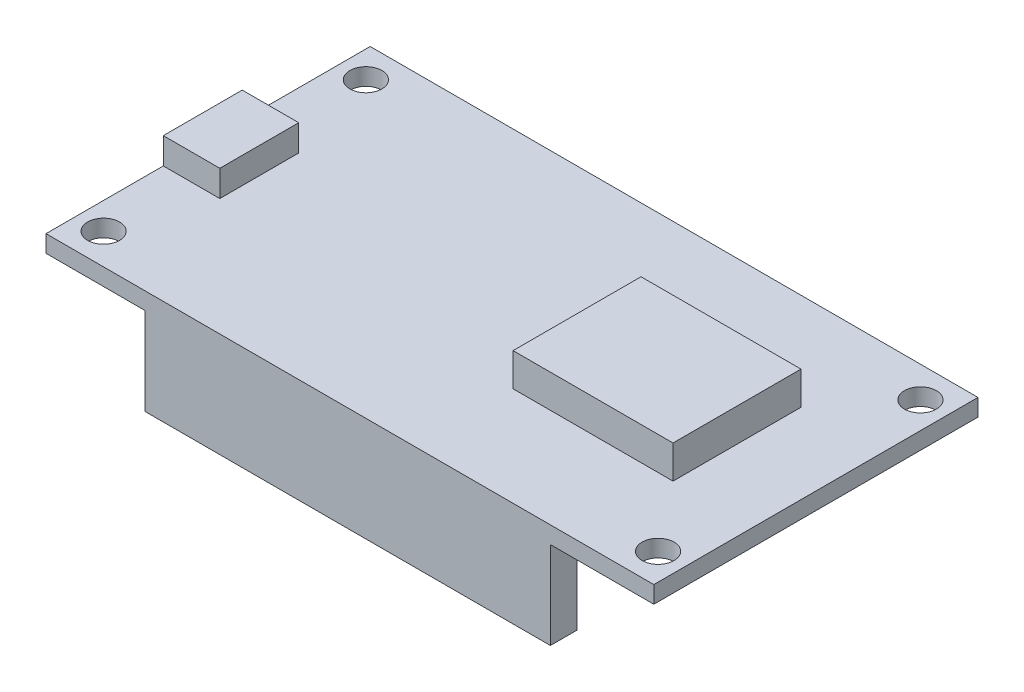
SolidWorks part; units mm, degrees
ref_plane "前视基准面" through (0, 0, 0) normal (0, 0, 1) x (1, 0, 0)
ref_plane "上视基准面" through (0, 0, 0) normal (0, 1, 0) x (1, 0, 0)
ref_plane "右视基准面" through (0, 0, 0) normal (1, 0, 0) x (0, 0, -1)
sketch "草图1" plane through (0, 0, 0) normal (0, 1, 0) x (1, 0, 0)
  line L1 (-19.4001, 13.152) -> (37.5999, 13.152)
  line L2 (-19.4001, 13.152) -> (-19.4001, -17.248)
  line L3 (-19.4001, -17.248) -> (37.5999, -17.248)
  line L4 (37.5999, 13.152) -> (37.5999, -17.248)
  dimension "D1" = 57
  dimension "D2" = 30.4
extrude "凸台-拉伸1" add sketch "草图1" along normal blind 1.6
sketch "草图2" plane through (0, 1.6, 0) normal (0, 1, 0) x (1, 0, 0)
  line L0 (37.5999, -17.248) -> (37.5999, 13.152) construction
  line L1 (15.0999, 4.052) -> (30.0999, 4.052)
  line L2 (15.0999, 4.052) -> (15.0999, -7.948)
  line L3 (15.0999, -7.948) -> (30.0999, -7.948)
  line L4 (30.0999, 4.052) -> (30.0999, -7.948)
  line L5 (37.5999, 13.152) -> (-19.4001, 13.152) construction
  dimension "D1" = 12
  dimension "D2" = 15
  dimension "D3" = 7.5
  dimension "D4" = 9.1
extrude "凸台-拉伸2" add sketch "草图2" along normal blind 3.1
sketch "草图3" plane through (0, 1.6, 0) normal (0, 1, 0) x (1, 0, 0)
  line L0 (-19.4001, 13.152) -> (-19.4001, -17.248) construction
  line L1 (-19.4001, 1.152) -> (-14.1001, 1.152)
  line L2 (-19.4001, 1.152) -> (-19.4001, -6.248)
  line L3 (-19.4001, -6.248) -> (-14.1001, -6.248)
  line L4 (-14.1001, 1.152) -> (-14.1001, -6.248)
  line L5 (37.5999, 13.152) -> (-19.4001, 13.152) construction
  line L6 (-19.4001, -17.248) -> (37.5999, -17.248) construction
  dimension "D1" = 0
  dimension "D2" = 5.3
  dimension "D3" = 7.4
  dimension "D4" = 12
  dimension "D5" = 11
extrude "凸台-拉伸3" add sketch "草图3" along normal blind 2.46
sketch "草图4" plane through (0, 1.6, 0) normal (0, 1, 0) x (1, 0, 0)
  line L0 (37.5999, 13.152) -> (-19.4001, 13.152) construction
  line L1 (-19.4001, 13.152) -> (-19.4001, 1.152) construction
  line L2 (-19.4001, -6.248) -> (-19.4001, -17.248) construction
  line L3 (-19.4001, -17.248) -> (37.5999, -17.248) construction
  line L4 (37.5999, -17.248) -> (37.5999, 13.152) construction
  circle A0 centre (-16.9001, 10.252) radius 1.5
  circle A1 centre (-16.9001, -14.348) radius 1.5
  circle A2 centre (35.0999, -14.348) radius 1.5
  circle A3 centre (35.0999, 10.252) radius 1.5
  dimension "D1" = 3
  dimension "D2" = 3
  dimension "D3" = 3
  dimension "D4" = 3
  dimension "D5" = 2.9
  dimension "D6" = 2.5
  dimension "D7" = 2.5
  dimension "D8" = 2.9
  dimension "D9" = 2.9
  dimension "D10" = 2.5
  dimension "D11" = 2.5
  dimension "D12" = 2.9
extrude "切除-拉伸1" cut sketch "草图4" against normal through all
sketch "草图5" plane through (0, 0, 0) normal (0, -1, 0) x (1, 0, 0)
  line L0 (-19.4001, 17.248) -> (37.5999, 17.248) construction
  line L1 (-10.1001, 17.248) -> (27.8999, 17.248)
  line L2 (-10.1001, 17.248) -> (-10.1001, 14.748)
  line L3 (-10.1001, 14.748) -> (27.8999, 14.748)
  line L4 (27.8999, 17.248) -> (27.8999, 14.748)
  line L5 (37.5999, 17.248) -> (37.5999, -13.152) construction
  line L6 (-19.4001, -13.152) -> (-19.4001, 17.248) construction
  line L7 (37.5999, -13.152) -> (-19.4001, -13.152) construction
  line L8 (-10.1001, -10.652) -> (27.8999, -10.652)
  line L9 (-10.1001, -10.652) -> (-10.1001, -13.152)
  line L10 (-10.1001, -13.152) -> (27.8999, -13.152)
  line L11 (27.8999, -10.652) -> (27.8999, -13.152)
  dimension "D1" = 2.5
  dimension "D2" = 38
  dimension "D3" = 0
  dimension "D4" = 9.7
  dimension "D5" = 9.3
  dimension "D6" = 0
  dimension "D7" = 2.5
  dimension "D8" = 9.7
  dimension "D9" = 38
extrude "凸台-拉伸4" add sketch "草图5" along normal blind 8.2
